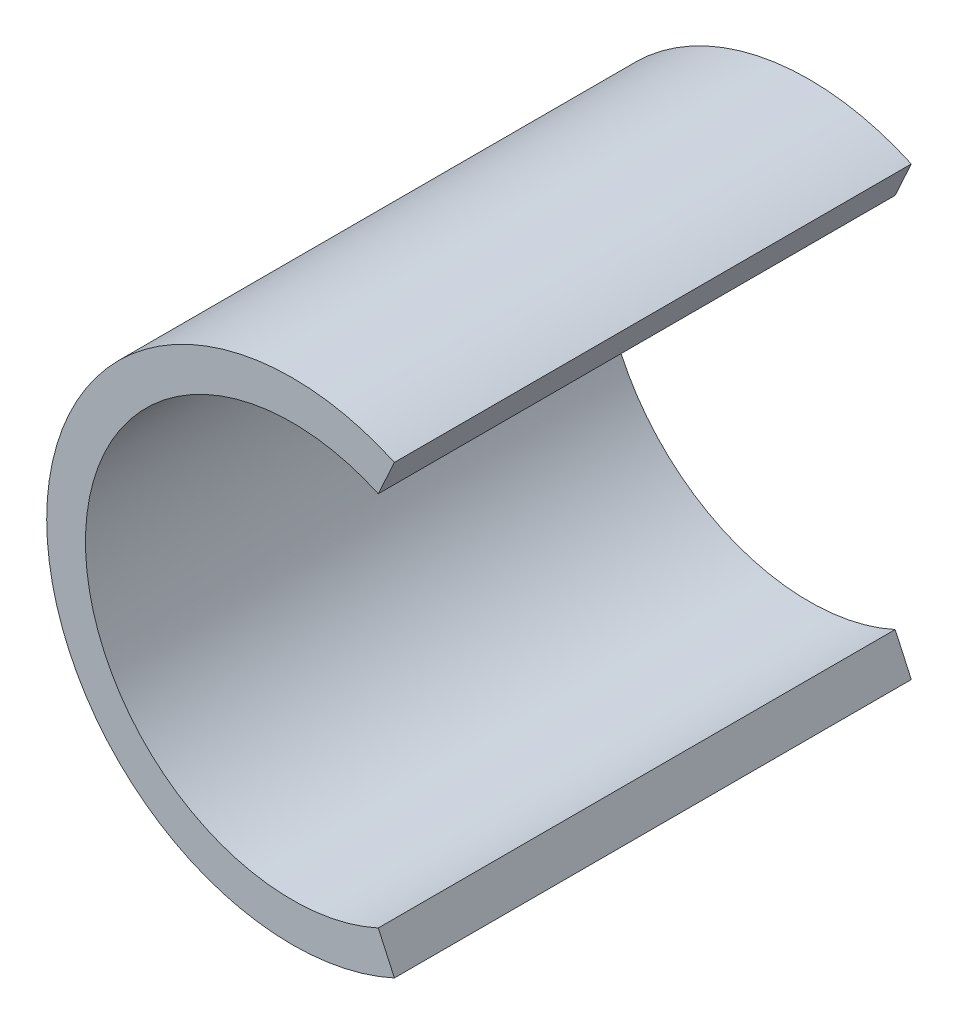
SolidWorks part; units mm, degrees
ref_plane "Front Plane" through (0, 0, 0) normal (0, 0, 1) x (1, 0, 0)
ref_plane "Top Plane" through (0, 0, 0) normal (0, 1, 0) x (1, 0, 0)
ref_plane "Right Plane" through (0, 0, 0) normal (1, 0, 0) x (0, 0, -1)
sketch "Sketch1" plane through (0, 0, 0) normal (0, 0, 1) x (1, 0, 0)
  circle A0 centre (0, 0) radius 4
  circle A1 centre (0, 0) radius 4.75
  dimension "D1" = 8
  dimension "D2" = 9.5
extrude "Boss-Extrude1" add sketch "Sketch1" along normal blind 10
sketch "Sketch3" plane through (0, 0, 10) normal (0, 0, 1) x (1, 0, 0)
  line L0 (0, 0) -> (5.5064, 0) construction
  line L1 (4, 0) -> (4.75, 0)
  line L2 (1.6645, 3.6372) -> (1.9766, 4.3192)
  line L3 (1.6645, -3.6372) -> (1.9766, -4.3192)
  circle A0 centre (0, 0) radius 4 construction
  circle A1 centre (0, 0) radius 4.75
  circle A2 centre (0, 0) radius 4.75
  circle A3 centre (0, 0) radius 4
  arc A4 (4, 0) -> (1.6645, 3.6372) centre (0, 0) ccw
  arc A5 (1.9766, 4.3192) -> (4.75, 0.0148) centre (0, 0) cw
  circle M5 centre (0, 0) radius 4.75
  circle M6 centre (0, 0) radius 4
  dimension "D1" = 0
extrude "Cut-Extrude2" cut sketch "Sketch3" against normal blind 10 contours L2 L1 A2 M6 M5 | L3 L1 M6 M5
ref_plane "Plane1" through (-4.5, 0, 0) normal (1, 0, 0) x (0, 0, -1)
sketch "Sketch4" plane through (-4.5, 0, 0) normal (1, 0, 0) x (0, 0, -1)
  line L1 (-1.0293, 0.7913) -> (-9.2034, 0.7913)
  line L2 (-1.0293, 0.7913) -> (-1.0293, -0.791)
  line L3 (-1.0293, -0.791) -> (-9.2034, -0.791)
  line L4 (-9.2034, 0.7913) -> (-9.2034, -0.791)
  point P5 (-5.1164, -0.791)
  dimension "D1" = 8.1742
  dimension "D2" = 1.5823
  dimension "D3" = 1.0293
  dimension "D4" = 0.7913
extrude "Boss-Extrude2" add sketch "Sketch4" against normal blind 0.5
sketch "Sketch5" plane through (-5, 0, 0) normal (-1, 0, 0) x (0, 0, 1)
  line L4 (9.2034, 0.7913) -> (1.0293, 0.7913)
  line L5 (9.2034, -0.791) -> (9.2034, 0.7913)
  line L6 (1.0293, -0.791) -> (9.2034, -0.791)
  line L7 (1.0293, 0.7913) -> (1.0293, -0.791)
  line L8 (9.2034, 0.7913) -> (1.0293, 0.7913)
  line L9 (9.2034, -0.791) -> (9.2034, 0.7913)
  line L10 (1.0293, -0.791) -> (9.2034, -0.791)
  line L11 (1.0293, 0.7913) -> (1.0293, -0.791)
  point P2 (5.1164, -0.791)
  dimension "D1" = 0
